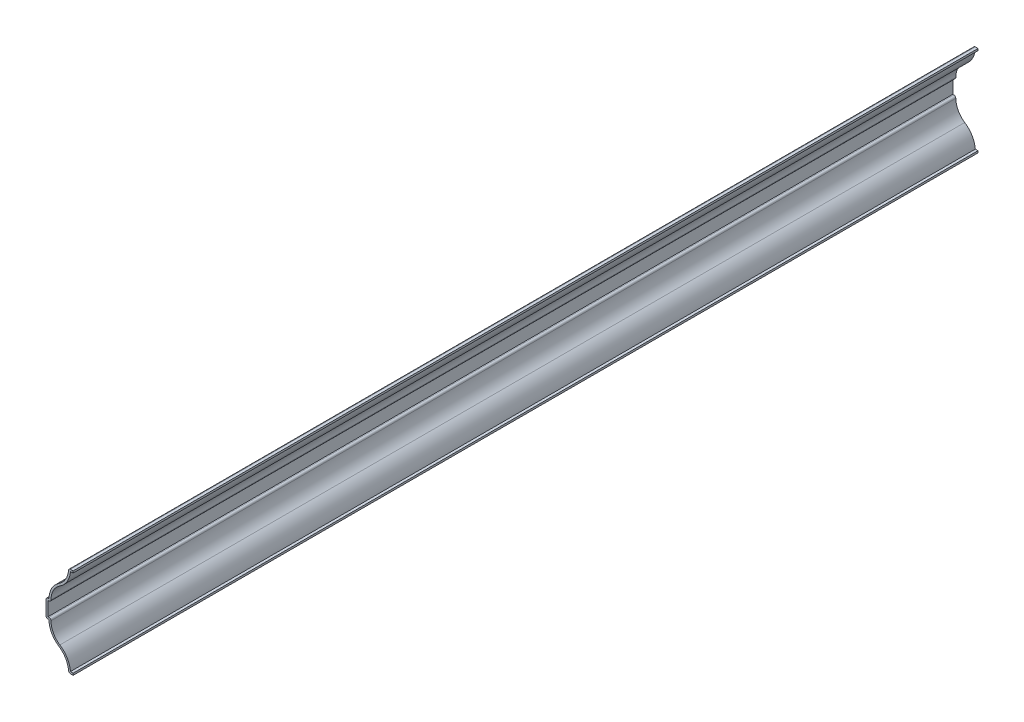
SolidWorks part; units mm, degrees
ref_plane "Front Plane" through (0, 0, 0) normal (0, 0, 1) x (1, 0, 0)
ref_plane "Top Plane" through (0, 0, 0) normal (0, 1, 0) x (1, 0, 0)
ref_plane "Right Plane" through (0, 0, 0) normal (1, 0, 0) x (0, 0, -1)
sketch "Sketch1" plane through (0, 0, 0) normal (0, 0, 1) x (1, 0, 0)
  line L0 (0, 0) -> (-2.3813, 0)
  line L1 (-12.7, 19.05) -> (-14.2875, 19.05)
  line L2 (-14.2875, 19.05) -> (-14.2875, 28.575)
  line L3 (0, 47.625) -> (-2.3813, 47.625)
  line L4 (-14.2875, 23.8125) -> (-17.0149, 23.8125) construction
  line L5 (-12.7, 28.575) -> (-14.2875, 28.575)
  arc A0 (-2.3813, 0) -> (-7.5406, 9.525) centre (-13.7532, 0) ccw
  arc A1 (-7.5406, 9.525) -> (-12.7, 19.05) centre (-1.328, 19.05) cw
  arc A2 (-2.3813, 47.625) -> (-7.5406, 38.1) centre (-13.7532, 47.625) cw
  arc A3 (-7.5406, 38.1) -> (-12.7, 28.575) centre (-1.328, 28.575) ccw
  point P17 (-7.541, 9.4605)
  point P18 (0, 0)
  dimension "D1" = 47.625
  dimension "D2" = 2.3813
  dimension "D3" = 1.5875
  dimension "D4" = 9.525
  dimension "D5" = 19.05
  dimension "D6" = 19.05
  dimension "D7" = 14.2875
  dimension "D8" = 10.3187
extrude "Extrude-Thin1" add sketch "Sketch1" against normal blind 476.25 thin
fillet "Fillet1" radius 1.016 6 edges at (-2.3813, 0, -238.125) (-11.634, 20.066, -238.125) (-14.2875, 19.05, -238.125) (-14.2875, 28.575, -238.125) (-11.634, 27.559, -238.125) (-2.3813, 47.625, -238.125)
